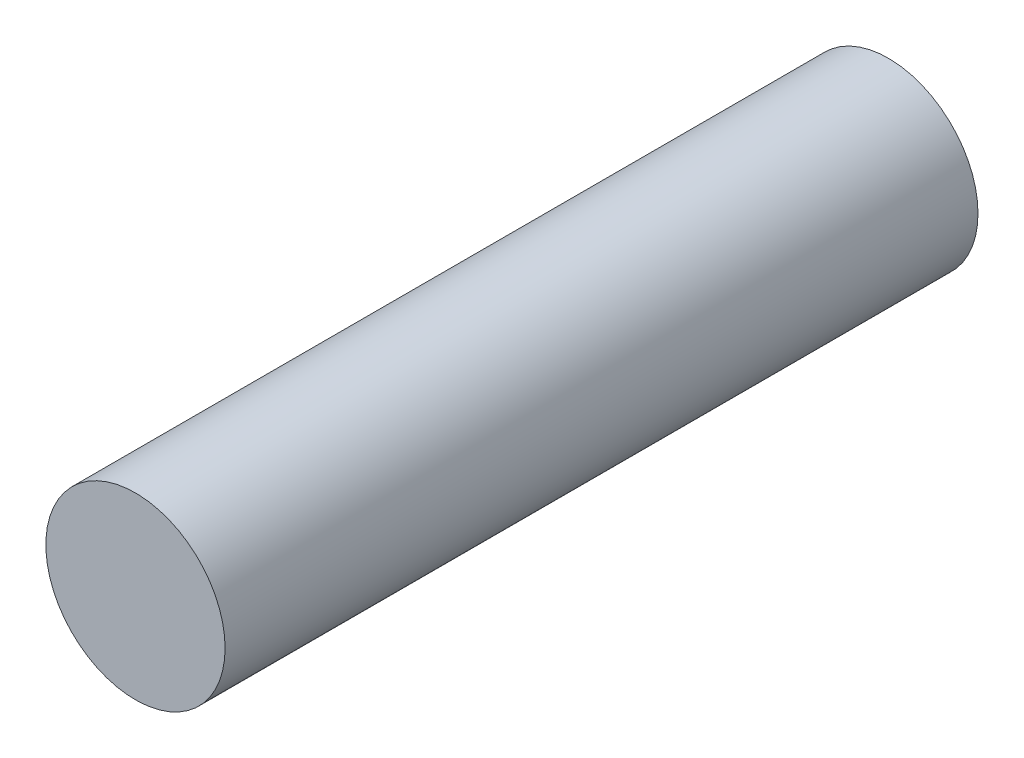
SolidWorks part; units mm, degrees
ref_plane "Front Plane" through (0, 0, 0) normal (0, 0, 1) x (1, 0, 0)
ref_plane "Top Plane" through (0, 0, 0) normal (0, 1, 0) x (1, 0, 0)
ref_plane "Right Plane" through (0, 0, 0) normal (1, 0, 0) x (0, 0, -1)
sketch "Sketch1" plane through (0, 0, 0) normal (0, 0, 1) x (1, 0, 0)
  circle A0 centre (0, 0) radius 7.5
  dimension "D1" = 15
extrude "Boss-Extrude1" add sketch "Sketch1" along normal blind 63
